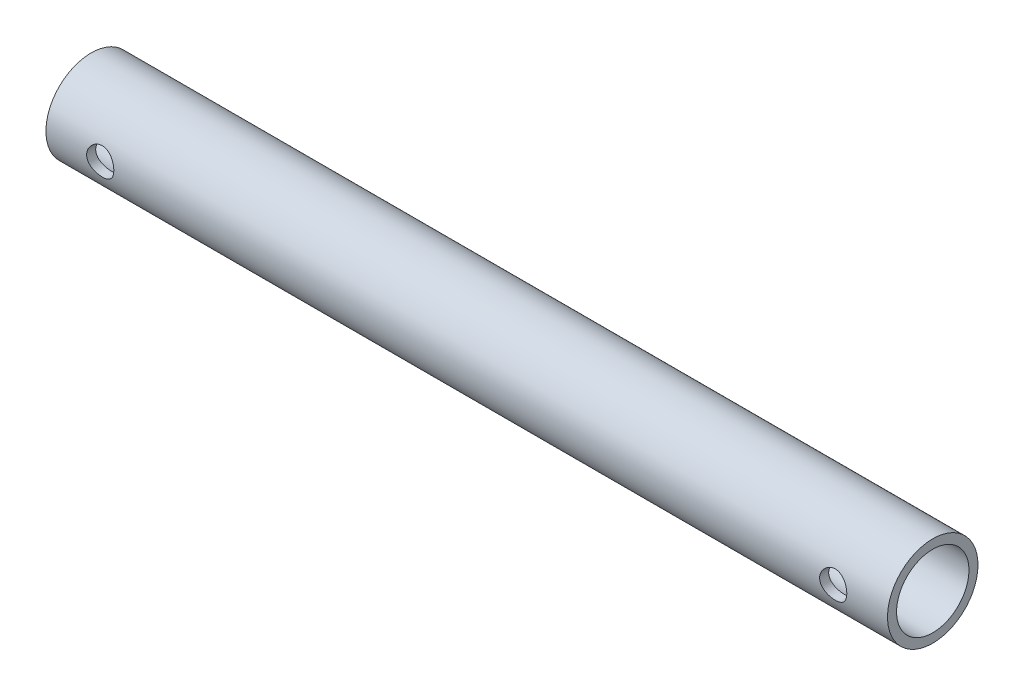
SolidWorks part; units mm, degrees
ref_plane "前视基准面" through (0, 0, 0) normal (0, 0, 1) x (1, 0, 0)
ref_plane "上视基准面" through (0, 0, 0) normal (0, 1, 0) x (1, 0, 0)
ref_plane "右视基准面" through (0, 0, 0) normal (1, 0, 0) x (0, 0, -1)
sketch "草图1" plane through (0, 0, 0) normal (1, 0, 0) x (0, 0, -1)
  circle A0 centre (0, 0) radius 5
  circle A1 centre (0, 0) radius 4
  dimension "D1" = 10
  dimension "D2" = 1
extrude "凸台-拉伸1" add sketch "草图1" along normal mid plane 93
sketch "草图2" plane through (0, 0, 0) normal (0, 0, 1) x (1, 0, 0)
  line L0 (0, 5) -> (0, -5) construction
  line L1 (46.5, 5) -> (-46.5, 5) construction
  line L2 (-46.5, -5) -> (46.5, -5) construction
  line L3 (36.5, 5) -> (36.5, -5) construction
  circle A0 centre (40.5, 0) radius 1.5
  circle A2 centre (-40.5, 0) radius 1.5
  point P12 (0, 0)
  point P13 (36.5, 0)
  point P14 (0, 0)
  point P15 (0, 0)
  dimension "D1" = 36.5
  dimension "D2" = 4
  dimension "D3" = 3
extrude "切除-拉伸1" cut sketch "草图2" against normal through all both and the other way through all
